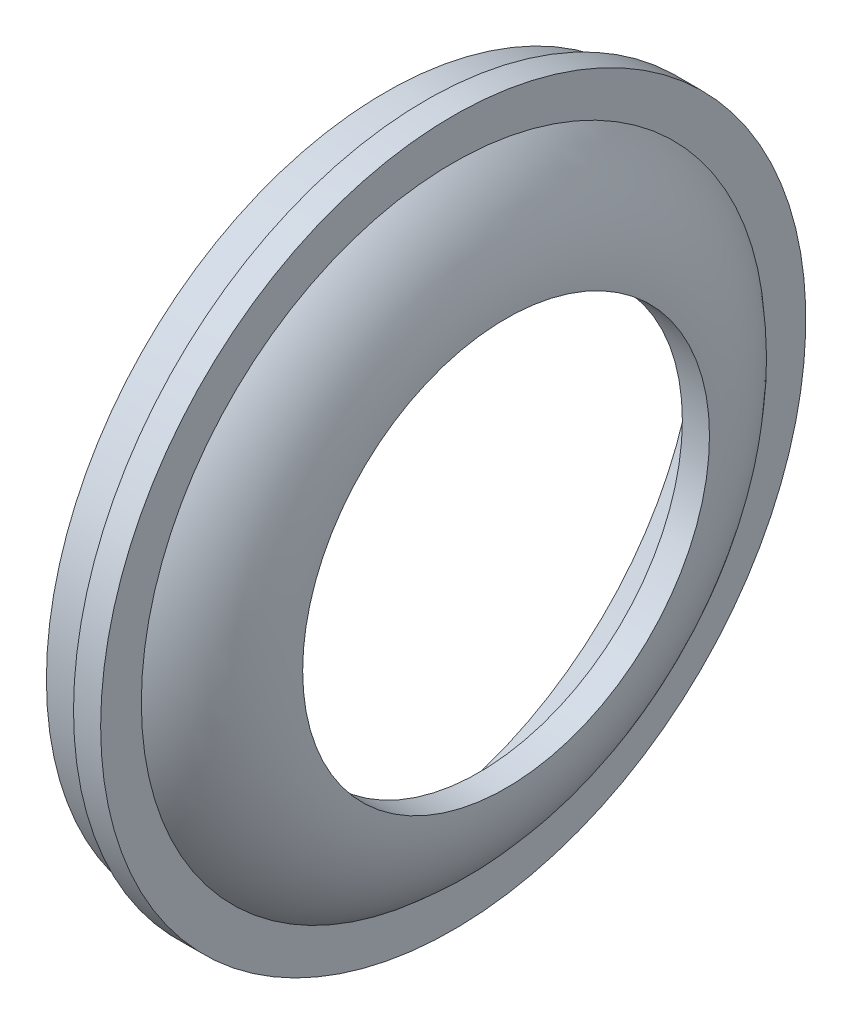
SolidWorks part; units mm, degrees
ref_plane "Front Plane" through (0, 0, 0) normal (0, 0, 1) x (1, 0, 0)
ref_plane "Top Plane" through (0, 0, 0) normal (0, 1, 0) x (1, 0, 0)
ref_plane "Right Plane" through (0, 0, 0) normal (1, 0, 0) x (0, 0, -1)
sketch "Sketch1" plane through (0, 0, 0) normal (0, 1, 0) x (1, 0, 0)
  line L0 (-17.3656, 0) -> (17.0094, 0) construction
  line L2 (1.5719, 25) -> (1.5719, 26)
  line L3 (1.5719, 26) -> (-0.4281, 26)
  line L4 (-0.4281, 26) -> (-0.4281, 25)
  line L6 (-0.4281, 25) -> (-3.4281, 25)
  line L7 (-3.4281, 25) -> (-3.4281, 23)
  line L10 (1.5719, 23) -> (1.5719, 25)
  line L11 (0.339, 21.4252) -> (-3.4281, 23)
  line L12 (5.4688, 15) -> (3.4688, 15)
  arc A0 (1.5719, 23) -> (5.4688, 15) centre (-4.6914, 15) cw
  arc A1 (0.339, 21.4252) -> (3.4688, 15) centre (-4.6914, 15) cw
  arc A3 (0.339, 21.4252) -> (0.339, 8.5748) centre (-4.6914, 15) cw construction
  arc A4 (1.5719, 23) -> (1.5719, 7) centre (-4.6914, 15) cw construction
  dimension "D1" = 2
  dimension "D2" = 1
  dimension "D3" = 2
  dimension "D4" = 50
  dimension "D6" = 30
  dimension "D7" = 3
  dimension "D5" = 2
revolve "Revolve1" add sketch "Sketch1" angle 360 about L0
